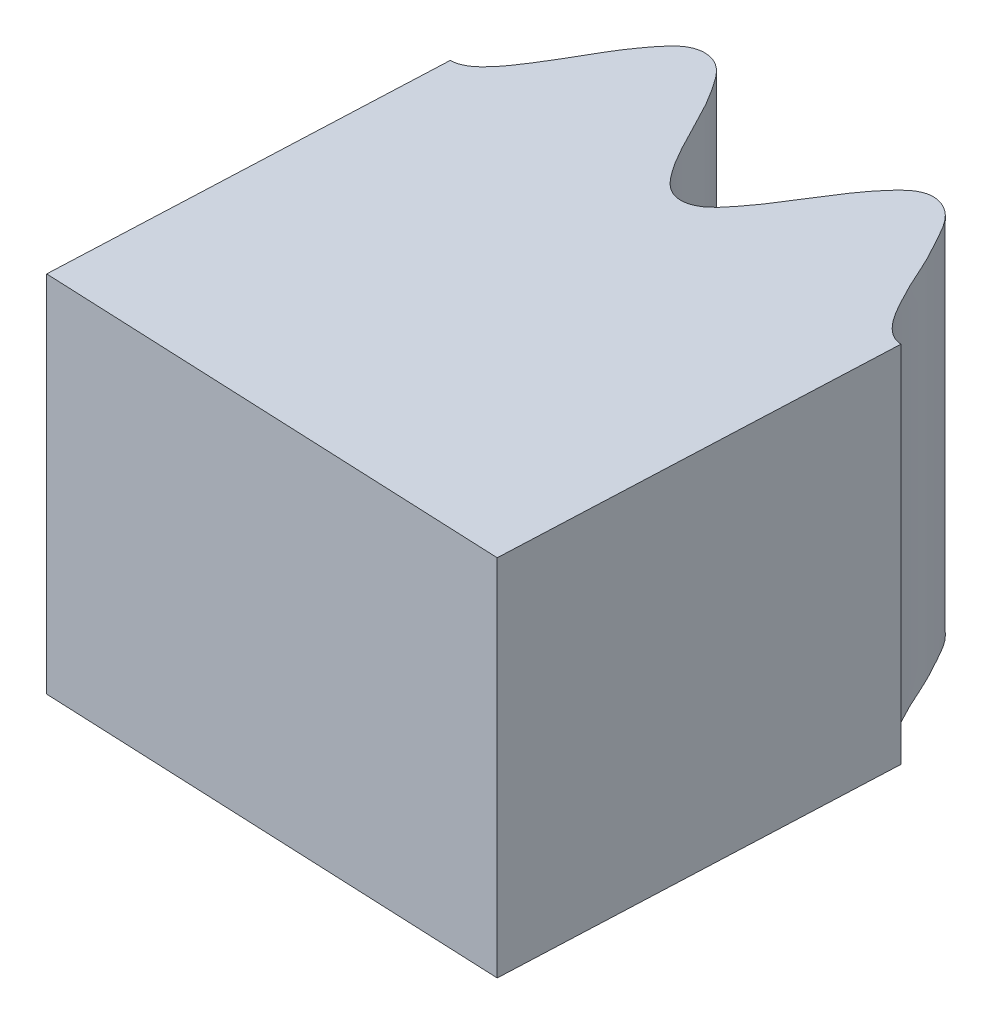
SolidWorks part; units mm, degrees
ref_plane "Front Plane" through (0, 0, 0) normal (0, 0, 1) x (1, 0, 0)
ref_plane "Top Plane" through (0, 0, 0) normal (0, 1, 0) x (1, 0, 0)
ref_plane "Right Plane" through (0, 0, 0) normal (1, 0, 0) x (0, 0, -1)
sketch "Sketch1" plane through (0, 0, 0) normal (0, 1, 0) x (1, 0, 0)
  line L0 (0, 75) -> (0, 70)
  line L1 (75, 0) -> (70, 0)
  arc A0 (0, 70) -> (70, 0) centre (0, 0) cw
  spline S0 degree 4 number of poles 779 (74.1673, -10.4775) -> (-10.5046, 74.3581) construction
  spline S1 degree 4 number of poles 657 (75, 0) -> (0, 75)
  dimension "D1" = 70
extrude "Boss-Extrude1" add sketch "Sketch1" along normal blind 4
sketch "Sketch2" plane through (0, 4, 0) normal (0, 1, 0) x (1, 0, 0)
  line L0 (0.648, 74.2496) -> (0.4624, 69.9985)
  line L1 (0, 75) -> (0, 70) construction
  line L2 (0, 75) -> (0, 70)
  arc A0 (70, 0) -> (0, 70) centre (0, 0) ccw construction
  arc A2 (0.4624, 69.9985) -> (0, 70) centre (0, 0) ccw
  spline S2 degree 4 number of poles 657 (75, 0) -> (0, 75) construction
  dimension "D2" = 0.5
  dimension "D1" = 2.5
extrude "Cut-Extrude1" cut sketch "Sketch2" against normal through all both and the other way through all
sketch "Sketch3" plane through (0, 4, 0) normal (0, 1, 0) x (1, 0, 0)
  line L0 (5.6402, 69.7724) -> (5.8258, 74.0238)
  line L1 (0.4624, 69.9985) -> (0.648, 74.2496) construction
  line L2 (70, 0) -> (75, 0) construction
  line L3 (70, 0) -> (75, 0)
  arc A0 (70, 0) -> (0.4624, 69.9985) centre (0, 0) ccw construction
  arc A1 (70, 0) -> (5.6402, 69.7724) centre (0, 0) ccw
  spline S1 degree 4 number of poles 653 (75, 0) -> (0.648, 74.2496) construction
  dimension "D1" = 4
extrude "Cut-Extrude2" cut sketch "Sketch3" against normal through all both and the other way through all
sketch "Sketch4" plane through (0, 0, 0) normal (0, 1, 0) x (1, 0, 0)
  line L0 (0.4624, 69.9985) -> (5.6402, 69.7724)
  arc A0 (5.6402, 69.7724) -> (0.4624, 69.9985) centre (0, 0) ccw construction
  arc A1 (5.6402, 69.7724) -> (0.4624, 69.9985) centre (0, 0) ccw
extrude "Boss-Extrude2" add sketch "Sketch4" along normal up to surface (4 mm away) up to face at (3.7918, 4, -71.9948)
ref_plane "Plane1" through (0, 0, 0) normal (0.999, 0, 0.0436) x (0.0436, 0, -0.999)
